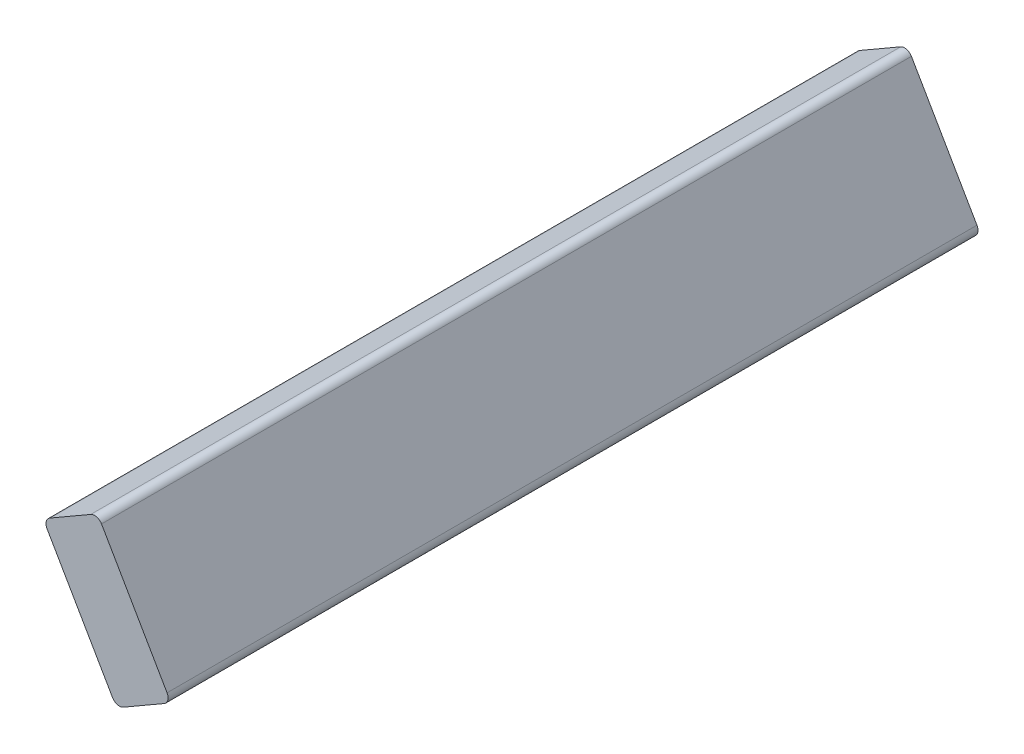
SolidWorks part; units mm, degrees
material "Pine"
ref_plane "Front Plane" through (0, 0, 0) normal (0, 0, 1) x (1, 0, 0)
ref_plane "Top Plane" through (0, 0, 0) normal (0, 1, 0) x (1, 0, 0)
ref_plane "Right Plane" through (0, 0, 0) normal (1, 0, 0) x (0, 0, -1)
sketch "Sketch1" plane through (0, 0, 0) normal (0, 0, 1) x (1, 0, 0)
  line L0 (227.6934, -470.5765) -> (183.2434, -393.5868)
  line L1 (227.6934, -470.5765) -> (260.6889, -451.5265)
  line L2 (183.2434, -393.5868) -> (216.2389, -374.5368)
  line L3 (260.6889, -451.5265) -> (216.2389, -374.5368)
  line L4 (330.2409, -571.9939) -> (260.6889, -451.5265) construction
extrude "Boss-Extrude1" add sketch "Sketch1" along normal up to surface (490.538 mm away)
fillet "Fillet1" radius 4.7625 4 edges at (227.6934, -470.5765, 245.269) (183.2434, -393.5868, 245.269) (216.2389, -374.5368, 245.269) (260.6889, -451.5265, 245.269)
